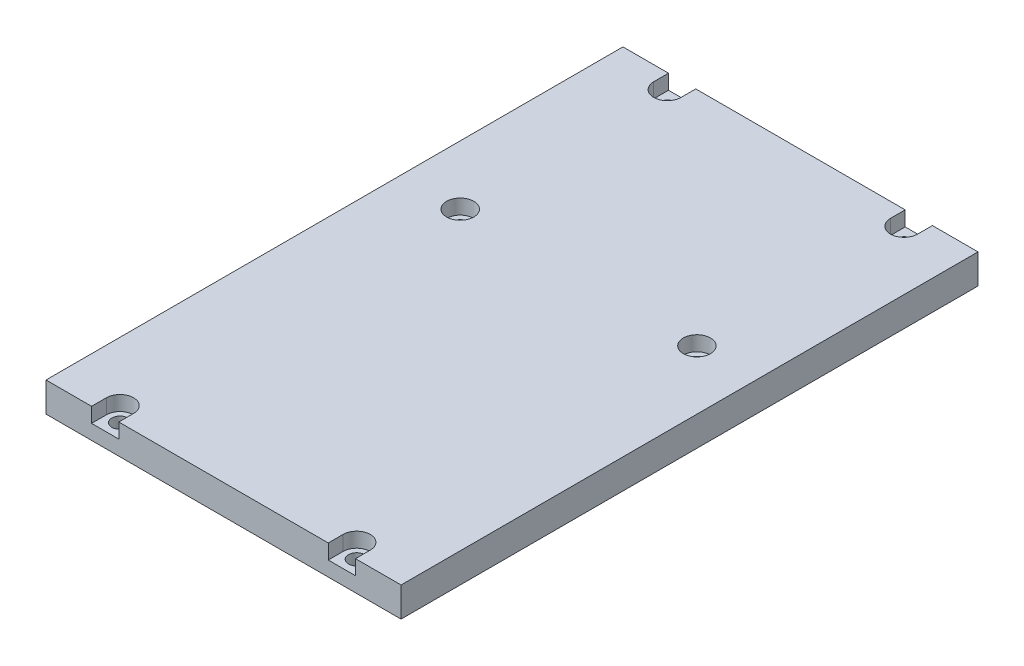
SolidWorks part; units mm, degrees
ref_plane "Front" through (0, 0, 0) normal (0, 0, 1) x (1, 0, 0)
ref_plane "Top" through (0, 0, 0) normal (0, 1, 0) x (1, 0, 0)
ref_plane "Right" through (0, 0, 0) normal (1, 0, 0) x (0, 0, -1)
sketch "Sketch1" plane through (0, 0, 0) normal (0, 1, 0) x (1, 0, 0)
  line L1 (-77.4278, 71.2487) -> (42.5722, 71.2487)
  line L2 (-77.4278, 71.2487) -> (-77.4278, -123.7513)
  line L3 (-77.4278, -123.7513) -> (42.5722, -123.7513)
  line L4 (42.5722, 71.2487) -> (42.5722, -123.7513)
  dimension "D1" = 120
  dimension "D2" = 195
extrude "Boss-Extrude1" add sketch "Sketch1" along normal blind 10
sketch "Sketch2" plane through (0, 10, 0) normal (0, 1, 0) x (-1, 0, 0)
  line L0 (77.4278, 123.7513) -> (-42.5722, 123.7513) construction
  line L1 (-42.5722, 123.7513) -> (-42.5722, -71.2487) construction
  line L2 (-42.5722, -71.2487) -> (77.4278, -71.2487) construction
  line L3 (77.4278, -71.2487) -> (77.4278, 123.7513) construction
  circle A0 centre (-22.5722, 118.7513) radius 2.75
  circle A1 centre (57.4278, 118.7513) radius 2.75
  circle A2 centre (-22.5722, 3.7513) radius 2.75
  circle A3 centre (57.4278, 3.7513) radius 2.75
  circle A4 centre (-22.5722, -66.2487) radius 2.75
  circle A5 centre (57.4278, -66.2487) radius 2.75
  dimension "D1" = 5.5
  dimension "D2" = 5
  dimension "D3" = 20
  dimension "D4" = 5
  dimension "D5" = 70
  dimension "D6" = 20
extrude "Cut-Extrude1" cut sketch "Sketch2" against normal through all
sketch "Sketch3" plane through (0, 10, 0) normal (0, 1, 0) x (1, 0, 0)
  line L0 (-62.0278, 66.2487) -> (-62.0278, 71.2487)
  line L1 (42.5722, 71.2487) -> (-77.4278, 71.2487) construction
  line L2 (-62.0278, 71.2487) -> (-52.8278, 71.2487)
  line L3 (-52.8278, 71.2487) -> (-52.8278, 66.2487)
  line L4 (17.9722, 66.2487) -> (17.9722, 71.2487)
  line L5 (17.9722, 71.2487) -> (27.1722, 71.2487)
  line L6 (27.1722, 66.2487) -> (27.1722, 71.2487)
  line L7 (-62.0278, -118.7513) -> (-62.0278, -123.7513)
  line L8 (-77.4278, -123.7513) -> (42.5722, -123.7513) construction
  line L9 (-62.0278, -123.7513) -> (-52.8278, -123.7513)
  line L10 (-52.8278, -123.7513) -> (-52.8278, -118.7513)
  line L11 (17.9722, -118.7513) -> (17.9722, -123.7513)
  line L12 (17.9722, -123.7513) -> (27.1722, -123.7513)
  line L13 (27.1722, -123.7513) -> (27.1722, -118.7513)
  arc A0 (27.1722, -118.7513) -> (17.9722, -118.7513) centre (22.5722, -118.7513) ccw
  arc A1 (-52.8278, -118.7513) -> (-62.0278, -118.7513) centre (-57.4278, -118.7513) ccw
  circle A2 centre (22.5722, -3.7513) radius 4.6
  circle A3 centre (-57.4278, -3.7513) radius 4.6
  arc A4 (17.9722, 66.2487) -> (27.1722, 66.2487) centre (22.5722, 66.2487) ccw
  arc A5 (-62.0278, 66.2487) -> (-52.8278, 66.2487) centre (-57.4278, 66.2487) ccw
  dimension "D1" = 9.2
extrude "Cut-Extrude2" cut sketch "Sketch3" against normal blind 5
